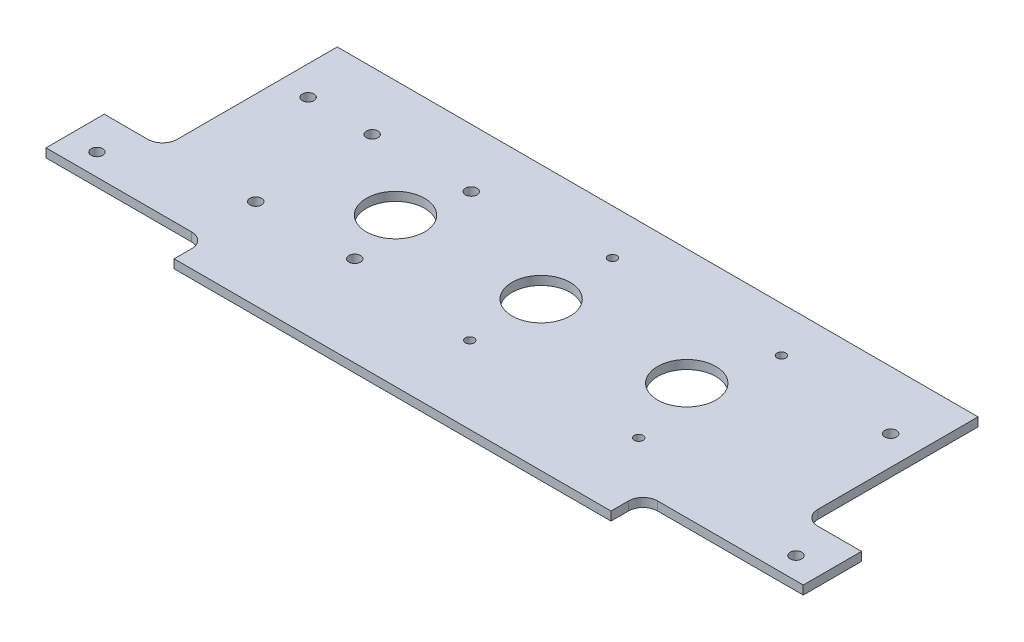
SolidWorks part; units mm, degrees
ref_plane "Front Plane" through (0, 0, 0) normal (0, 0, 1) x (1, 0, 0)
ref_plane "Top Plane" through (0, 0, 0) normal (0, 1, 0) x (1, 0, 0)
ref_plane "Right Plane" through (0, 0, 0) normal (1, 0, 0) x (0, 0, -1)
sketch "Sketch1" plane through (0, 0, 0) normal (0, 1, 0) x (1, 0, 0)
  line L1 (110, -40) -> (-110, -40)
  line L2 (110, -40) -> (110, 40)
  line L3 (110, 40) -> (-110, 40)
  line L4 (-110, -40) -> (-110, 40)
  line L5 (110, -40) -> (-110, 40) construction
  line L6 (110, 40) -> (-110, -40) construction
  point P0 (0, 0)
  dimension "D1" = 220
  dimension "D2" = 80
extrude "Boss-Extrude1" add sketch "Sketch1" along normal blind 3
sketch "Sketch2" plane through (0, 3, 0) normal (0, 1, 0) x (1, 0, 0)
  line L1 (-110, -40) -> (-130, -40)
  line L2 (-110, -40) -> (-110, -20)
  line L3 (-110, -20) -> (-130, -20)
  line L4 (-130, -40) -> (-130, -20)
  circle A0 centre (-120, -32.5) radius 2
  dimension "D3" = 7.5
  dimension "D4" = 120
  dimension "D1" = 20
  dimension "D2" = 20
extrude "Boss-Extrude2" add sketch "Sketch2" against normal blind 3
mirror "Mirror1" about plane through (0, 0, 0) normal (1, 0, 0) of "Boss-Extrude2"
fillet "Fillet1" radius 5 2 edges at (-110, 1.5, 20) (110, 1.5, 20)
sketch "Sketch3" plane through (0, 3, 0) normal (0, 1, 0) x (1, 0, 0)
  line L0 (-110, 40) -> (-110, -15) construction
  line L1 (110, 40) -> (-110, 40) construction
  line L2 (0, -1.65) -> (0, 1.65) construction
  circle A0 centre (-100, 20) radius 2
  circle A1 centre (100, 20) radius 2
  dimension "D1" = 10
  dimension "D2" = 20
extrude "Cut-Extrude1" cut sketch "Sketch3" against normal blind 3
sketch "Sketch4" plane through (0, 3, 0) normal (0, 1, 0) x (1, 0, 0)
  line L0 (-1.65, 0) -> (1.65, 0) construction
  circle A0 centre (0, 24.5) radius 1.5
  circle A1 centre (58, 24.5) radius 1.5
  circle A2 centre (58, -24.5) radius 1.5
  circle A3 centre (0, -24.5) radius 1.5
  dimension "D1" = 58
  dimension "D2" = 0
  dimension "D3" = 24.5
  dimension "D4" = 3
  dimension "D5" = 3
extrude "Cut-Extrude2" cut sketch "Sketch4" against normal blind 3
sketch "Sketch5" plane through (0, 3, 0) normal (0, 1, 0) x (1, 0, 0)
  line L0 (-130, -40) -> (130, -40) construction
  line L1 (75, -51) -> (-75, -51)
  line L2 (75, -51) -> (75, -29)
  line L3 (75, -29) -> (-75, -29)
  line L4 (-75, -51) -> (-75, -29)
  line L5 (75, -51) -> (-75, -29) construction
  line L6 (75, -29) -> (-75, -51) construction
  point P0 (0, -40)
  dimension "D1" = 150
  dimension "D2" = 22
extrude "Boss-Extrude3" add sketch "Sketch5" against normal blind 3
fillet "Fillet2" radius 5 2 edges at (75, 1.5, 40) (-75, 1.5, 40)
sketch "Sketch6" plane through (0, 3, 0) normal (0, 1, 0) x (1, 0, 0)
  circle A0 centre (-50, 0) radius 10
  circle A1 centre (0, 0) radius 10
  circle A2 centre (50, 0) radius 10
  dimension "D1" = 50
  dimension "D2" = 50
extrude "Cut-Extrude3" cut sketch "Sketch6" against normal blind 3
sketch "Sketch7" plane through (0, 3, 0) normal (0, 1, 0) x (1, 0, 0)
  line L0 (-1.65, 0) -> (1.65, 0) construction
  line L1 (-110, 40) -> (-110, -15) construction
  circle A0 centre (-78, 20) radius 2
  circle A1 centre (-44, 20) radius 2
  circle A2 centre (-44, -20) radius 2
  circle A3 centre (-78, -20) radius 2
  dimension "D1" = 34
  dimension "D2" = 32
extrude "Cut-Extrude4" cut sketch "Sketch7" against normal blind 3
